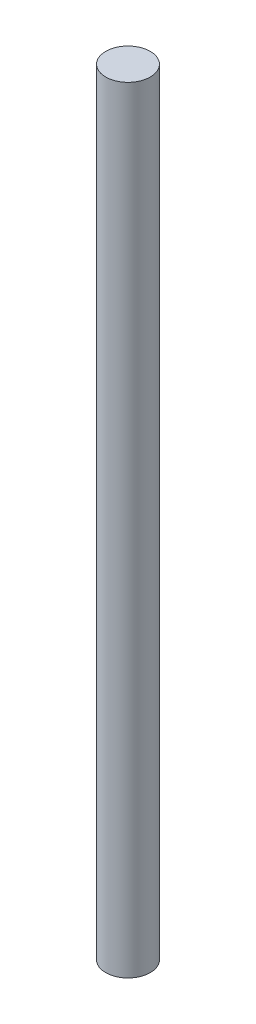
SolidWorks part; units mm, degrees
ref_plane "Front" through (0, 0, 0) normal (0, 0, 1) x (1, 0, 0)
ref_plane "Top" through (0, 0, 0) normal (0, 1, 0) x (1, 0, 0)
ref_plane "Right" through (0, 0, 0) normal (1, 0, 0) x (0, 0, -1)
sketch "Sketch1" plane through (0, 0, 0) normal (0, 1, 0) x (1, 0, 0)
  circle A0 centre (0, 0) radius 1.55
  dimension "D1" = 3.1
extrude "Boss-Extrude1" add sketch "Sketch1" along normal blind 54
